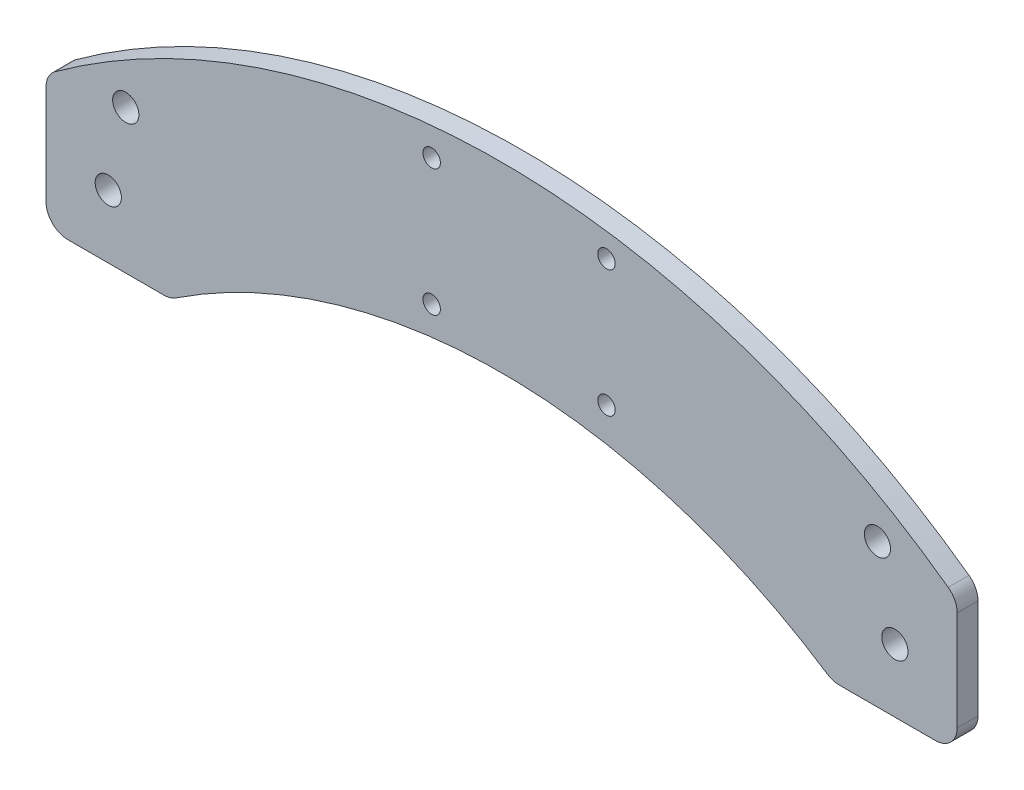
SolidWorks part; units mm, degrees
ref_plane "Front Plane" through (0, 0, 0) normal (0, 0, 1) x (1, 0, 0)
ref_plane "Top Plane" through (0, 0, 0) normal (0, 1, 0) x (1, 0, 0)
ref_plane "Right Plane" through (0, 0, 0) normal (1, 0, 0) x (0, 0, -1)
sketch "Sketch1" plane through (0, 0, 0) normal (0, 0, 1) x (1, 0, 0)
  line L0 (-14.25, -9.45) -> (-14.25, 13.3361)
  line L4 (194.25, 13.3361) -> (194.25, -9.45)
  line L5 (189.25, -14.45) -> (167.2697, -14.45)
  line L9 (12.7303, -14.45) -> (-9.25, -14.45)
  line L10 (14.25, -32.1) -> (14.25, 6.9127) construction
  line L11 (194.25, 14.25) -> (194.25, -14.45) construction
  line L12 (194.25, -14.45) -> (185.75, -32.1) construction
  line L13 (165.75, -32.1) -> (165.75, 6.9127) construction
  circle A0 centre (74, 43.4) radius 2
  circle A1 centre (74, 14.4) radius 2
  circle A2 centre (114, 43.4) radius 2
  circle A3 centre (114, 14.4) radius 2
  circle A4 centre (180, 0) radius 3
  circle A5 centre (0, 0) radius 3
  arc A6 (164.5101, -13.6195) -> (15.4899, -13.6195) centre (90, -126.195) ccw
  arc A7 (-12.1864, 17.383) -> (192.1864, 17.383) centre (90, -123.45) cw
  circle A8 centre (4, 18.4) radius 3
  circle A9 centre (176, 18.4) radius 3
  arc A10 (194.25, -9.45) -> (189.25, -14.45) centre (189.25, -9.45) cw
  arc A11 (-14.25, -9.45) -> (-9.25, -14.45) centre (-9.25, -9.45) ccw
  arc A12 (167.2697, -14.45) -> (164.5101, -13.6195) centre (167.2697, -9.45) cw
  arc A13 (15.4899, -13.6195) -> (12.7303, -14.45) centre (12.7303, -9.45) cw
  arc A14 (194.25, 13.3361) -> (192.1864, 17.383) centre (189.25, 13.3361) ccw
  arc A15 (-12.1864, 17.383) -> (-14.25, 13.3361) centre (-9.25, 13.3361) ccw
  point P56 (194.25, -14.45)
  point P59 (-14.25, -14.45)
  point P62 (165.75, -14.45)
  point P65 (14.25, -14.45)
  dimension "D1" = 6
  dimension "D2" = 4
  dimension "D3" = 135
  dimension "D4" = 65
  dimension "D5" = 6
  dimension "D6" = 174
  dimension "D7" = 5
  dimension "D8" = 5
  dimension "D9" = 5
  dimension "D10" = 5
  dimension "D11" = 14.45
  dimension "D12" = 14.25
extrude "Boss-Extrude1" add sketch "Sketch1" along normal blind 4.7625
sketch "Sketch3" plane through (0, 0, 4.7625) normal (0, 0, 1) x (1, 0, 0)
  line L0 (12.1832, 18.3831) -> (7.9246, -1.2063)
  line L1 (68, 37.2983) -> (68, 22.5399)
  line L2 (120, 35.748) -> (120, 21.5772)
  line L3 (167.8982, 18.0087) -> (172.0754, -1.2063)
  line L4 (13.9111, 26.3314) -> (68, 13.0781) construction
  line L5 (166.0889, 26.3314) -> (120, 11.5766) construction
  line L6 (154.7404, 25.8483) -> (126.5245, 16.8153)
  line L7 (134.874, 13.1884) -> (161.4879, 21.7085)
  line L8 (49.1834, 14.6) -> (18.259, 22.1773)
  line L9 (26.6707, 26.2937) -> (61.8101, 17.6836)
  arc A0 (161.4879, 21.7085) -> (167.8982, 18.0087) centre (163.0123, 16.9465) cw
  arc A1 (120, 35.748) -> (126.0736, 40.6314) centre (125, 35.748) cw
  arc A2 (167.8217, -8.6161) -> (12.1783, -8.6161) centre (90, -126.195) ccw
  arc A3 (164.546, -6.5125) -> (134.8348, 7.4869) centre (90, -126.195) ccw
  circle A4 centre (4, 18.4) radius 3 construction
  arc A5 (188.6627, 12.5267) -> (-8.6627, 12.5267) centre (90, -123.45) ccw
  arc A6 (154.9861, 31.4719) -> (126.0736, 40.6314) centre (90, -123.45) ccw
  circle A7 centre (0, 0) radius 3 construction
  circle A8 centre (180, 0) radius 3 construction
  circle A9 centre (176, 18.4) radius 3 construction
  circle A10 centre (114, 43.4) radius 2 construction
  circle A11 centre (74, 43.4) radius 2 construction
  arc A12 (62.1718, 42.2292) -> (26.2462, 31.9831) centre (90, -123.45) ccw
  arc A13 (49.3347, 8.8137) -> (15.454, -6.5125) centre (90, -126.195) ccw
  arc A14 (120, 21.5772) -> (126.5245, 16.8153) centre (125, 21.5772) ccw
  arc A15 (68, 37.2983) -> (62.1718, 42.2292) centre (63, 37.2983) ccw
  arc A16 (68, 22.5399) -> (61.8101, 17.6836) centre (63, 22.5399) cw
  arc A17 (18.259, 22.1773) -> (12.1832, 18.3831) centre (17.0691, 17.321) ccw
  arc A18 (154.7404, 25.8483) -> (154.9861, 31.4719) centre (153.8257, 28.7055) ccw
  arc A19 (134.874, 13.1884) -> (134.8348, 7.4869) centre (135.7887, 10.3312) ccw
  arc A20 (49.1834, 14.6) -> (49.3347, 8.8137) centre (48.4694, 11.6862) cw
  arc A21 (26.6707, 26.2937) -> (26.2462, 31.9831) centre (27.3847, 29.2075) cw
  arc A22 (164.546, -6.5125) -> (172.0754, -1.2063) centre (167.1895, -2.2685) ccw
  arc A23 (15.454, -6.5125) -> (7.9246, -1.2063) centre (12.8105, -2.2685) cw
  point P46 (68, 43.1033)
  dimension "D6" = 8
  dimension "D8" = 6
  dimension "D13" = 5
  dimension "D14" = 3
  dimension "D15" = 5
  dimension "D3" = 8
  dimension "D4" = 8
  dimension "D5" = 8
  dimension "D7" = 6
  dimension "D9" = 3
  dimension "D10" = 6
  dimension "D11" = 3
  dimension "D12" = 6
  dimension "D1" = 6
  dimension "D2" = 6
extrude "Cut-Extrude1" [suppressed] cut sketch "Sketch3" against normal offset from surface (4.35 mm away) 2
sketch "Sketch4" plane through (0, 0, 0) normal (0, 0, 1) x (1, 0, 0)
  line L0 (170, 10) -> (190, -10) construction
  line L1 (-10, 10) -> (10, 10)
  line L2 (-10, 10) -> (-10, -10)
  line L3 (-10, -10) -> (10, -10)
  line L4 (10, 10) -> (10, -10)
  line L5 (170, 10) -> (190, 10)
  line L6 (170, 10) -> (170, -10)
  line L7 (170, -10) -> (190, -10)
  line L8 (190, 10) -> (190, -10)
  line L9 (-10, 10) -> (10, -10) construction
  dimension "D1" = 20
extrude "Cut-Extrude2" cut sketch "Sketch4" along normal blind 0.01
